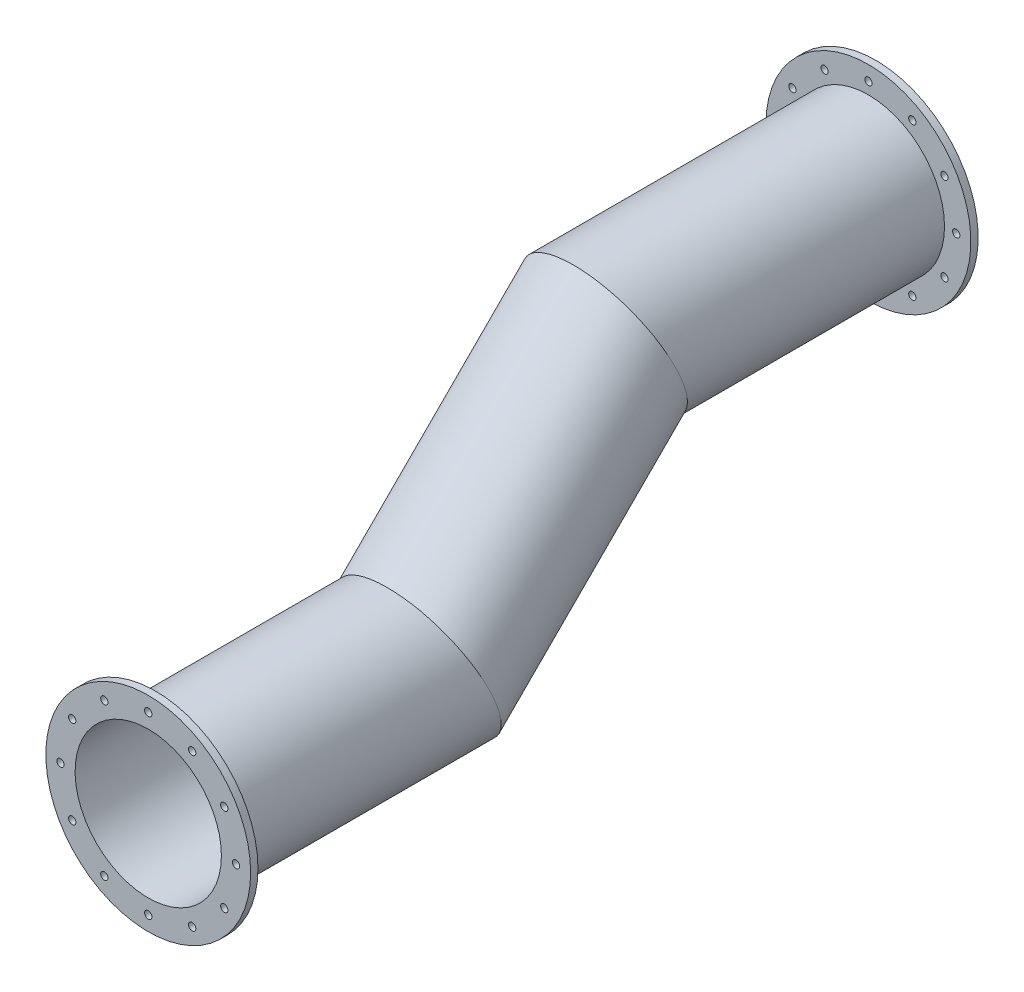
SolidWorks part; units mm, degrees
ref_plane "Front Plane" through (0, 0, 0) normal (0, 0, 1) x (1, 0, 0)
ref_plane "Top Plane" through (0, 0, 0) normal (0, 1, 0) x (1, 0, 0)
ref_plane "Right Plane" through (0, 0, 0) normal (1, 0, 0) x (0, 0, -1)
sketch "Sketch2" plane through (0, 0, 0) normal (0, 0, 1) x (1, 0, 0)
  circle A0 centre (0, 0) radius 50
  dimension "D1" = 100
sketch "Sketch3" plane through (0, 0, 0) normal (1, 0, 0) x (0, 0, -1)
  line L0 (0, 0) -> (180, 0)
  line L1 (180, 0) -> (307.2792, 127.2792)
  line L2 (307.2792, 127.2792) -> (487.2792, 127.2792)
  point P3 (497.5015, 129.9493)
  dimension "D1" = 45
  dimension "D2" = 180
sweep "Sweep-Thin1" add profiles "Sketch2" path "Sketch3" parameters "D1"=2
sketch "Sketch4" plane through (0, 0, 0) normal (0, 0, 1) x (1, 0, 0)
  circle A0 centre (0, 0) radius 50 construction
  circle A1 centre (0, 0) radius 50
  circle A2 centre (0, 0) radius 70
  circle A3 centre (0, -60) radius 2.5
  circle A4 centre (-30, -51.9615) radius 2.5
  circle A5 centre (-51.9615, -30) radius 2.5
  circle A6 centre (-60, 0) radius 2.5
  circle A7 centre (-51.9615, 30) radius 2.5
  circle A8 centre (-30, 51.9615) radius 2.5
  circle A9 centre (0, 60) radius 2.5
  circle A10 centre (30, 51.9615) radius 2.5
  circle A11 centre (51.9615, 30) radius 2.5
  circle A12 centre (60, 0) radius 2.5
  circle A13 centre (51.9615, -30) radius 2.5
  circle A14 centre (30, -51.9615) radius 2.5
  point P5 (0, 0)
  point P8 (-55.466, -23.3341)
  point P9 (0, 0)
  point P31 (0, 0)
  dimension "data" = 140
  dimension "D3" = 5
  dimension "D2" = 60
  dimension "D4" = 12
extrude "Boss-Extrude1" add sketch "Sketch4" along normal blind 5
sketch "Sketch5" plane through (0, 0, -487.2792) normal (0, 0, -1) x (-1, 0, 0)
  circle A0 centre (0, 127.2792) radius 50 construction
  circle A1 centre (0, 127.2792) radius 50
  circle A2 centre (0, 127.2792) radius 70
  circle A3 centre (0, 67.2792) radius 2.5
  circle A4 centre (-30, 75.3177) radius 2.5
  circle A5 centre (-51.9615, 97.2792) radius 2.5
  circle A6 centre (-60, 127.2792) radius 2.5
  circle A7 centre (-51.9615, 157.2792) radius 2.5
  circle A8 centre (-30, 179.2407) radius 2.5
  circle A9 centre (0, 187.2792) radius 2.5
  circle A10 centre (30, 179.2407) radius 2.5
  circle A11 centre (51.9615, 157.2792) radius 2.5
  circle A12 centre (60, 127.2792) radius 2.5
  circle A13 centre (51.9615, 97.2792) radius 2.5
  circle A14 centre (30, 75.3177) radius 2.5
  point P7 (0, 127.2792)
  point P30 (0, 127.2792)
  dimension "D1" = 140
  dimension "D2" = 5
  dimension "D3" = 60
  dimension "D4" = 12
extrude "Boss-Extrude2" add sketch "Sketch5" along normal blind 5
